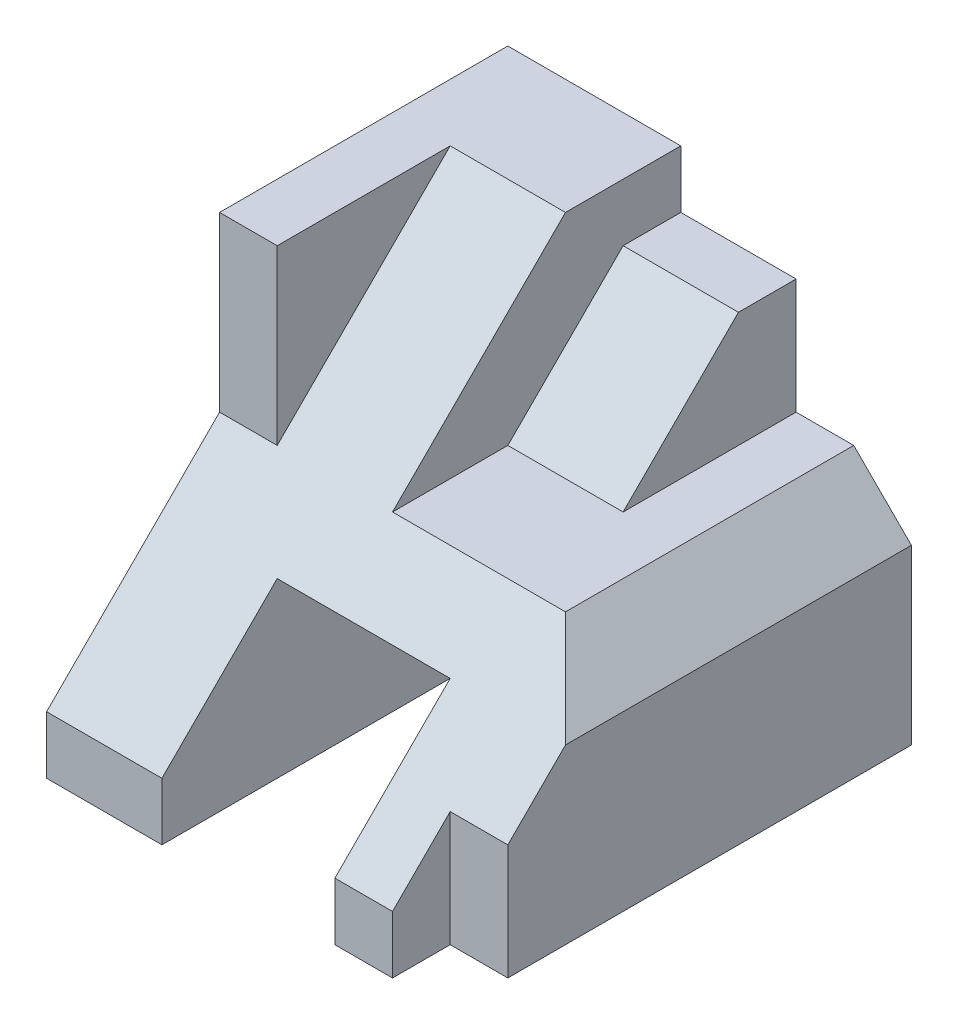
SolidWorks part; units mm, degrees
ref_plane "Front Plane" through (0, 0, 0) normal (0, 0, 1) x (1, 0, 0)
ref_plane "Top Plane" through (0, 0, 0) normal (0, 1, 0) x (1, 0, 0)
ref_plane "Right Plane" through (0, 0, 0) normal (1, 0, 0) x (0, 0, -1)
sketch "Sketch1" plane through (0, 0, 0) normal (0, 0, 1) x (1, 0, 0)
  line L1 (3.5, -3.5) -> (-3.5, -3.5)
  line L2 (3.5, -3.5) -> (3.5, 3.5)
  line L3 (3.5, 3.5) -> (-3.5, 3.5)
  line L4 (-3.5, -3.5) -> (-3.5, 3.5)
  line L5 (3.5, -3.5) -> (-3.5, 3.5) construction
  line L6 (3.5, 3.5) -> (-3.5, -3.5) construction
  point P0 (0, 0)
  dimension "D1" = 7
  dimension "D2" = 7
extrude "Boss-Extrude1" add sketch "Sketch1" along normal blind 8
sketch "Sketch2" plane through (0, 0, 8) normal (0, 0, 1) x (1, 0, 0)
  line L0 (-1.5, -3.5) -> (-1.5, -0.5)
  line L1 (-3.5, -3.5) -> (3.5, -3.5) construction
  line L2 (-1.5, -0.5) -> (1.5, -0.5)
  line L3 (1.5, -0.5) -> (1.5, -3.5)
  line L4 (1.5, -3.5) -> (-1.5, -3.5)
  dimension "D1" = 2
  dimension "D2" = 2
  dimension "D3" = 3
extrude "Cut-Extrude1" cut sketch "Sketch2" against normal through all
sketch "Sketch3" plane through (3.5, 0, 0) normal (1, 0, 0) x (0, 0, -1)
  line L0 (-8, -2.5) -> (-2, 3.5)
  line L1 (-8, -3.5) -> (-8, 3.5) construction
  line L2 (-8, 3.5) -> (0, 3.5) construction
  line L3 (-2, 3.5) -> (-8, 3.5)
  line L4 (-8, 3.5) -> (-8, -2.5)
  dimension "D1" = 1
  dimension "D2" = 2
extrude "Cut-Extrude2" cut sketch "Sketch3" against normal blind 6
sketch "Sketch4" plane through (-2.5, 0, 0) normal (1, 0, 0) x (0, 0, -1)
  line L0 (-5, 3.5) -> (-5, 0.5)
  line L1 (-2, 3.5) -> (-8, 3.5) construction
  line L2 (-8, -2.5) -> (-2, 3.5) construction
  line L3 (-5, 0.5) -> (-8, -2.5)
  line L4 (-8, -2.5) -> (-8, 3.5)
  line L5 (-8, 3.5) -> (-5, 3.5)
  dimension "D1" = 3
extrude "Cut-Extrude3" cut sketch "Sketch4" against normal blind 6
sketch "Sketch5" plane through (3.5, 0, 0) normal (1, 0, 0) x (0, 0, -1)
  line L0 (-8, -3.5) -> (-7, -3.5)
  line L1 (-8, -3.5) -> (0, -3.5) construction
  line L2 (-7, -3.5) -> (-7, -1.5)
  line L3 (-8, -2.5) -> (-2, 3.5) construction
  line L4 (-7, -1.5) -> (-8, -1.5)
  line L5 (-8, -1.5) -> (-8, -3.5)
  dimension "D1" = 1
extrude "Cut-Extrude4" cut sketch "Sketch5" against normal blind 1
sketch "Sketch6" plane through (3.5, 0, 0) normal (1, 0, 0) x (0, 0, -1)
  line L0 (0, 3.5) -> (-2, 3.5)
  line L1 (-2, 3.5) -> (-5, 0.5)
  line L2 (-5, 0.5) -> (-3, 0.5)
  line L3 (-3, 0.5) -> (-1, 2.5)
  line L4 (-1, 2.5) -> (0, 2.5)
  line L5 (0, -3.5) -> (0, 3.5) construction
  line L6 (0, 2.5) -> (0, 3.5)
  dimension "D1" = 1
  dimension "D2" = 2
extrude "Cut-Extrude5" cut sketch "Sketch6" against normal blind 4
sketch "Sketch7" plane through (0, 2.5, 0) normal (0, 1, 0) x (1, 0, 0)
  line L0 (1.5, 0) -> (1.5, -3)
  line L1 (-0.5, 0) -> (3.5, 0) construction
  line L2 (-0.5, -3) -> (3.5, -3) construction
  line L3 (1.5, -3) -> (3.5, -3)
  line L4 (3.5, -3) -> (3.5, 0)
  line L5 (3.5, 0) -> (1.5, 0)
  dimension "D1" = 2
extrude "Cut-Extrude6" cut sketch "Sketch7" against normal blind 2
sketch "Sketch8" plane through (0, 0, 0) normal (0, 0, -1) x (-1, 0, 0)
  line L0 (-2.5, 0.5) -> (-3.5, -0.5)
  line L1 (-3.5, 0.5) -> (-1.5, 0.5) construction
  line L2 (-3.5, -3.5) -> (-3.5, 0.5) construction
  line L3 (-3.5, -0.5) -> (-3.5, 0.5)
  line L4 (-3.5, 0.5) -> (-2.5, 0.5)
  dimension "D1" = 1
extrude "Cut-Extrude7" cut sketch "Sketch8" against normal blind 6
